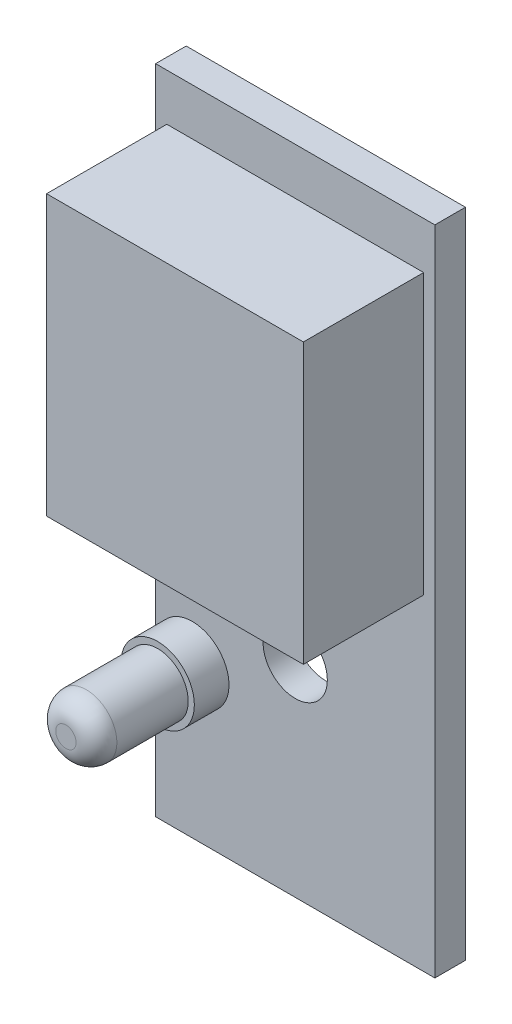
SolidWorks part; units mm, degrees
ref_plane "Front Plane" through (0, 0, 0) normal (0, 0, 1) x (1, 0, 0)
ref_plane "Top Plane" through (0, 0, 0) normal (0, 1, 0) x (1, 0, 0)
ref_plane "Right Plane" through (0, 0, 0) normal (1, 0, 0) x (0, 0, -1)
sketch "Sketch1" plane through (0, 0, 0) normal (0, 0, 1) x (1, 0, 0)
  line L1 (-6.85, 16) -> (6.85, 16)
  line L2 (-6.85, 16) -> (-6.85, -16)
  line L3 (-6.85, -16) -> (6.85, -16)
  line L4 (6.85, 16) -> (6.85, -16)
  point P0 (0, 0)
  dimension "D1" = 13.7
  dimension "D2" = 32
extrude "Boss-Extrude1" add sketch "Sketch1" along normal blind 1.5
sketch "Sketch2" plane through (0, 0, 1.5) normal (0, 0, 1) x (1, 0, 0)
  line L5 (6.3, 13.7) -> (6.3, 0)
  line L6 (6.3, 0) -> (-6.3, 0)
  line L7 (-6.3, 0) -> (-6.3, 13.7)
  line L8 (-6.3, 13.7) -> (6.3, 13.7)
extrude "Boss-Extrude2" add sketch "Sketch2" along normal blind 5.9
sketch "Sketch3" plane through (0, 0, 1.5) normal (0, 0, 1) x (1, 0, 0)
  circle A0 centre (-5.05, -8.6) radius 1.8
extrude "Boss-Extrude3" add sketch "Sketch3" along normal blind 1.7
sketch "Sketch6" plane through (0, 0, 3.2) normal (0, 0, 1) x (1, 0, 0)
  circle A0 centre (-5.05, -8.6) radius 1.5
  dimension "D1" = 3
extrude "Boss-Extrude4" add sketch "Sketch6" along normal blind 4.5
fillet "Fillet1" radius 1 1 edges at (-3.55, -8.6, 7.7)
sketch "Sketch7" plane through (0, 0, 1.5) normal (0, 0, 1) x (1, 0, 0)
  circle A0 centre (0, -5.975) radius 1.575
extrude "Cut-Extrude1" cut sketch "Sketch7" against normal through all
